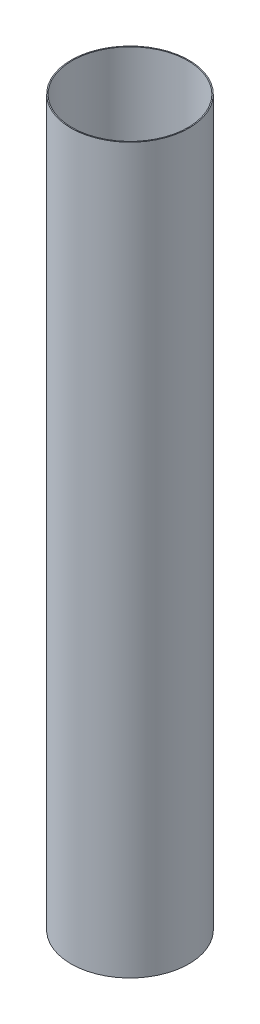
SolidWorks part; units mm, degrees
material "1060 Alloy"
ref_plane "Front Plane" through (0, 0, 0) normal (0, 0, 1) x (1, 0, 0)
ref_plane "Top Plane" through (0, 0, 0) normal (0, 1, 0) x (1, 0, 0)
ref_plane "Right Plane" through (0, 0, 0) normal (1, 0, 0) x (0, 0, -1)
sketch "Sketch1" plane through (0, 0, 0) normal (0, 1, 0) x (1, 0, 0)
  circle A0 centre (0, 0) radius 38.1
  circle A2 centre (0, 0) radius 37.465
  dimension "D1" = 76.2
  dimension "D2" = 74.93
extrude "Boss-Extrude1" add sketch "Sketch1" along normal blind 467.868
